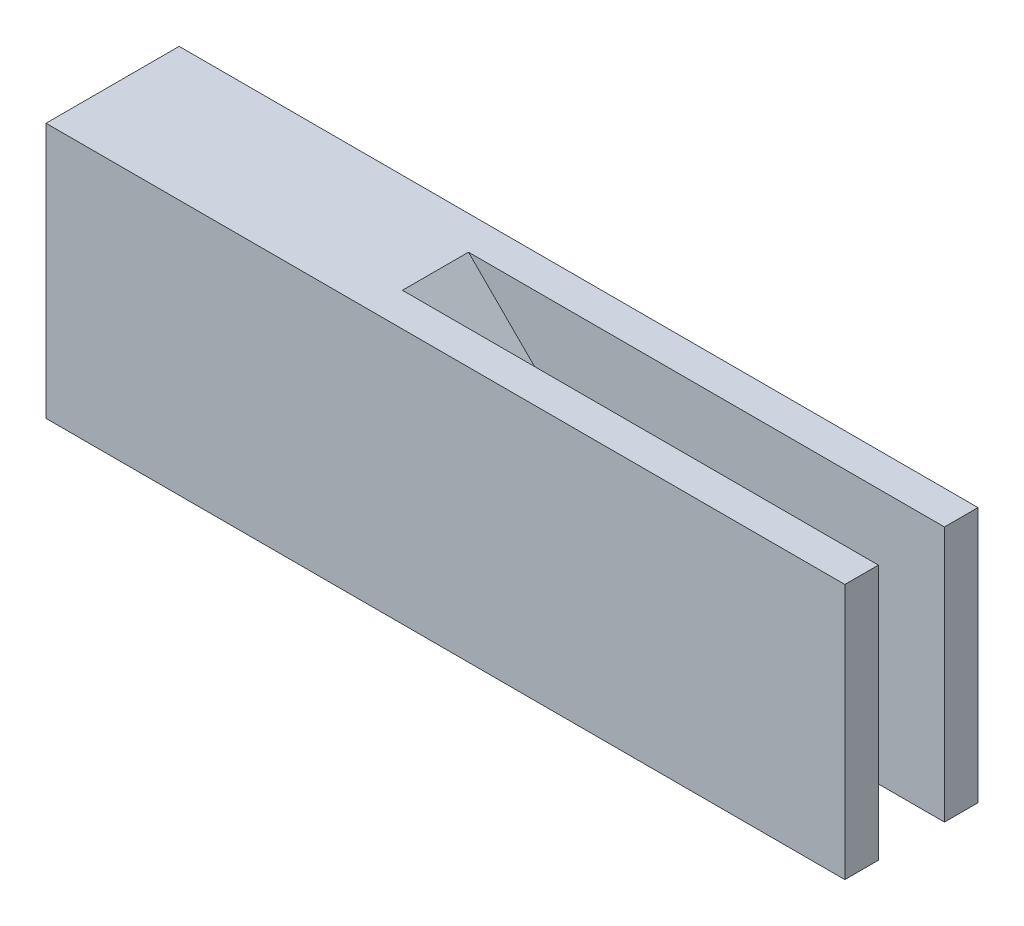
SolidWorks part; units mm, degrees
ref_plane "Front Plane" through (0, 0, 0) normal (0, 0, 1) x (1, 0, 0)
ref_plane "Top Plane" through (0, 0, 0) normal (0, 1, 0) x (1, 0, 0)
ref_plane "Right Plane" through (0, 0, 0) normal (1, 0, 0) x (0, 0, -1)
sketch "Sketch1" plane through (0, 0, 0) normal (1, 0, 0) x (0, 0, -1)
  line L1 (0, 0) -> (6.35, 0)
  line L2 (0, 0) -> (0, 12.192)
  line L3 (0, 12.192) -> (6.35, 12.192)
  line L4 (6.35, 0) -> (6.35, 12.192)
  dimension "D1" = 6.35
  dimension "D2" = 12.192
extrude "Boss-Extrude1" add sketch "Sketch1" along normal blind 25.4
sketch "Sketch2" plane through (25.4, 0, 0) normal (1, 0, 0) x (0, 0, -1)
  line L0 (0, 0) -> (6.35, 0) construction
  line L1 (0, 12.192) -> (1.6002, 12.192)
  line L2 (0, 12.192) -> (0, 0)
  line L3 (0, 0) -> (1.6002, 0)
  line L4 (1.6002, 12.192) -> (1.6002, 0)
  line L6 (6.35, 12.192) -> (4.7498, 12.192)
  line L7 (6.35, 12.192) -> (6.35, 0)
  line L8 (6.35, 0) -> (4.7498, 0)
  line L9 (4.7498, 12.192) -> (4.7498, 0)
  dimension "D1" = 1.6002
  dimension "D2" = 1.6002
extrude "Boss-Extrude2" add sketch "Sketch2" along normal blind 12.7
chamfer "Chamfer1" distance 10 angle 45 1 edges at (25.4, 12.192, -3.175)
